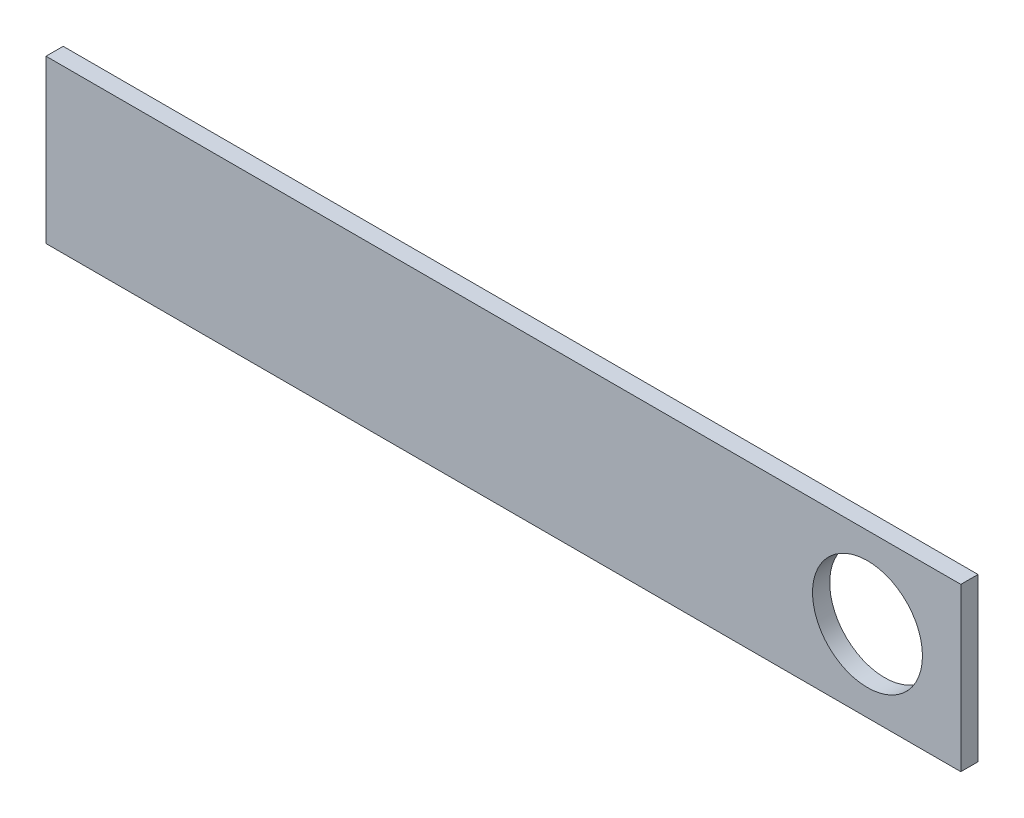
SolidWorks part; units mm, degrees
ref_plane "Front Plane" through (0, 0, 0) normal (0, 0, 1) x (1, 0, 0)
ref_plane "Top Plane" through (0, 0, 0) normal (0, 1, 0) x (1, 0, 0)
ref_plane "Right Plane" through (0, 0, 0) normal (1, 0, 0) x (0, 0, -1)
sketch "Sketch1" plane through (0, 0, 0) normal (0, 0, 1) x (1, 0, 0)
  line L1 (-67.8561, -48.7503) -> (67.4652, -48.7503)
  line L2 (-67.8561, -48.7503) -> (-67.8561, -72.7506)
  line L3 (-67.8561, -72.7506) -> (67.4652, -72.7506)
  line L4 (67.4652, -48.7503) -> (67.4652, -72.7506)
extrude "Boss-Extrude1" add sketch "Sketch1" against normal blind 2.54
sketch "Sketch2" plane through (0, 0, 0) normal (0, 0, 1) x (1, 0, 0)
  line L0 (67.4652, -60.7505) -> (53.6593, -60.7505) construction
  line L1 (67.4652, -72.7506) -> (67.4652, -48.7503) construction
  circle A0 centre (53.6593, -60.7505) radius 8.1301
extrude "Cut-Extrude1" cut sketch "Sketch2" against normal through all
